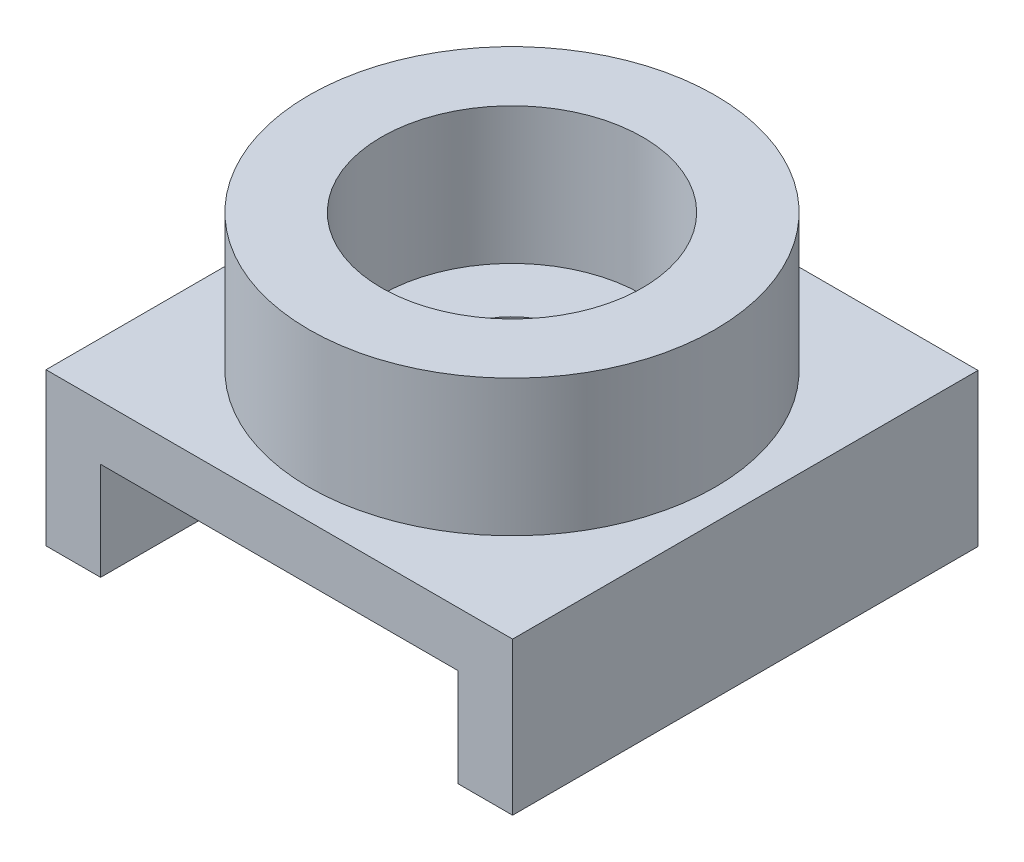
SolidWorks part; units mm, degrees
ref_plane "Front Plane" through (0, 0, 0) normal (0, 0, 1) x (1, 0, 0)
ref_plane "Top Plane" through (0, 0, 0) normal (0, 1, 0) x (1, 0, 0)
ref_plane "Right Plane" through (0, 0, 0) normal (1, 0, 0) x (0, 0, -1)
sketch "Sketch2" plane through (0, 0, 0) normal (0, 0, 1) x (1, 0, 0)
  line L0 (0, 0) -> (0, 2.0955) construction
  line L1 (-3.8227, 0) -> (-4.9911, 0)
  line L2 (-4.9911, 0) -> (-4.9911, 3.2639)
  line L3 (-4.9911, 3.2639) -> (4.9911, 3.2639)
  line L5 (3.8227, 2.0955) -> (-3.8227, 2.0955)
  line L6 (-3.8227, 2.0955) -> (-3.8227, 0)
  line L7 (3.8227, 2.0955) -> (3.8227, 0)
  line L8 (4.9911, 0) -> (4.9911, 3.2639)
  line L9 (3.8227, 0) -> (4.9911, 0)
  line L10 (0, 3.2639) -> (0, 50.7266) construction
  dimension "D1" = 1.1684
  dimension "D2" = 3.2639
  dimension "D3" = 9.9822
  dimension "D4" = 1.1684
extrude "Boss-Extrude1" add sketch "Sketch2" along normal mid plane 9.9568
sketch "Sketch3" plane through (0, 3.2639, 0) normal (0, 1, 0) x (1, 0, 0)
  circle A0 centre (0, 0) radius 4.3434
  circle A1 centre (0, 0) radius 2.794
  dimension "D1" = 8.6868
  dimension "D2" = 5.588
extrude "Boss-Extrude2" add sketch "Sketch3" along normal offset from surface (2.921 mm away) 6.1849 up to face at (-4.4069, 0, 0)
sketch "Sketch4" plane through (0, 3.2639, 0) normal (0, 1, 0) x (1, 0, 0)
  circle A0 centre (0, 0) radius 1.397
  dimension "D1" = 2.794
extrude "Cut-Extrude1" cut sketch "Sketch4" against normal up to next
